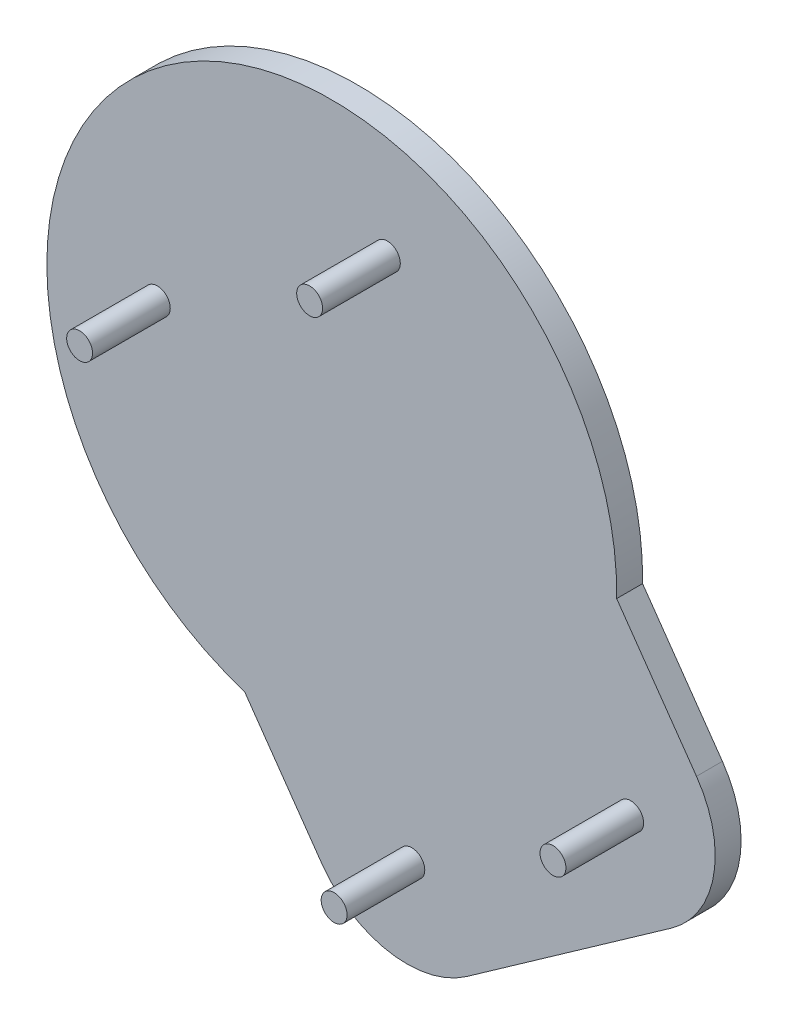
SolidWorks part; units mm, degrees
ref_plane "Front Plane" through (0, 0, 0) normal (0, 0, 1) x (1, 0, 0)
ref_plane "Top Plane" through (0, 0, 0) normal (0, 1, 0) x (1, 0, 0)
ref_plane "Right Plane" through (0, 0, 0) normal (1, 0, 0) x (0, 0, -1)
sketch "Sketch1" plane through (0, 0, 0) normal (0, 0, 1) x (1, 0, 0)
  line L3 (-57.6728, -5.1296) -> (-42.7357, -26.462)
  line L4 (-14.8327, -31.3395) -> (24.6963, -3.4863)
  line L5 (29.5593, 24.3342) -> (14.1527, 46.3372)
  arc A3 (14.1527, 46.3372) -> (-57.6728, -5.1296) centre (-40.8401, 47.2312) ccw
  arc A4 (-42.7357, -26.462) -> (-14.8327, -31.3395) centre (-26.3526, -14.9905) ccw
  arc A5 (24.6963, -3.4863) -> (29.5593, 24.3342) centre (13.1763, 12.8627) ccw
  circle A6 centre (16.8571, 11.4037) radius 2.5
  circle A7 centre (-25.3905, -17.5835) radius 2.5
  circle A8 centre (-74.5185, 51.775) radius 2.5
  circle A9 centre (-30.1155, 81.4789) radius 2.5
extrude "Boss-Extrude1" add sketch "Sketch1" along normal blind 5
sketch "Sketch3" plane through (0, 0, 5) normal (0, 0, 1) x (1, 0, 0)
  circle A0 centre (16.8571, 11.4037) radius 2.5 construction
  circle A1 centre (-25.3905, -17.5835) radius 2.5 construction
  circle A2 centre (-30.1155, 81.4789) radius 2.5 construction
  circle A3 centre (-74.5185, 51.775) radius 2.5 construction
  circle A4 centre (16.8571, 11.4037) radius 2.5
  circle A5 centre (-25.3905, -17.5835) radius 2.5
  circle A6 centre (-30.1155, 81.4789) radius 2.5
  circle A7 centre (-74.5185, 51.775) radius 2.5
extrude "Boss-Extrude2" add sketch "Sketch3" along normal blind 15 separate body
